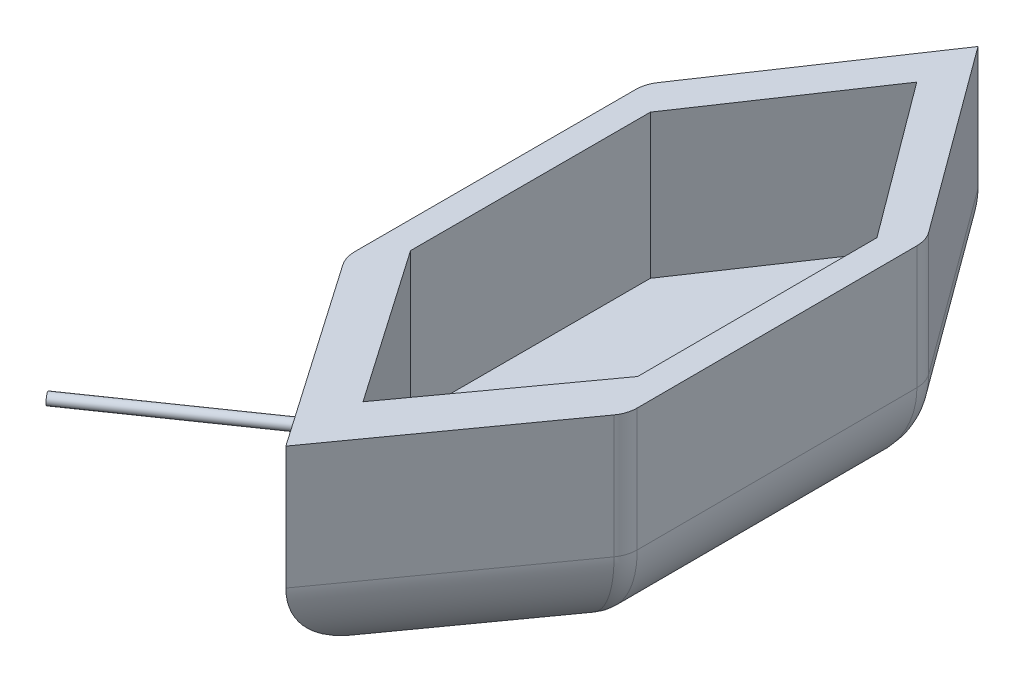
SolidWorks part; units mm, degrees
ref_plane "Front Plane" through (0, 0, 0) normal (0, 0, 1) x (1, 0, 0)
ref_plane "Top Plane" through (0, 0, 0) normal (0, 1, 0) x (1, 0, 0)
ref_plane "Right Plane" through (0, 0, 0) normal (1, 0, 0) x (0, 0, -1)
sketch "Sketch1" plane through (0, 0, 0) normal (0, 1, 0) x (1, 0, 0)
  line L0 (-53.4846, 104.1845) -> (-98.1583, 37.8199)
  line L2 (-6.1312, 39.7046) -> (-53.4846, 104.1845)
  line L3 (-98.1583, 37.8199) -> (-98.1583, -62.1801)
  line L5 (-53.4846, -126.6597) -> (-98.1583, -62.1801)
  line L6 (-5.8888, -60.2951) -> (-53.4846, -126.6597)
  line L7 (-6.1312, 39.7046) -> (-5.8888, -60.2951)
  dimension "D1" = 80
  dimension "D2" = 80
  dimension "D3" = 100
  dimension "D4" = 100
extrude "Boss-Extrude1" add sketch "Sketch1" along normal blind 71 contours L0 L3 L5 L6 L7 L2
sketch "Sketch2" plane through (0, 71, 0) normal (0, 1, 0) x (1, 0, 0)
  line L0 (-53.4193, 83.6901) -> (-89.1583, 30.5984)
  line L1 (-15.1128, 32.1086) -> (-53.4193, 83.6901)
  line L2 (-89.1583, 30.5984) -> (-89.1583, -49.4016)
  line L3 (-53.4193, -100.9853) -> (-89.1583, -49.4016)
  line L4 (-14.9189, -47.8912) -> (-53.4193, -100.9853)
  line L5 (-15.1128, 32.1086) -> (-14.9189, -47.8912)
  line L6 (-6.1312, 39.7046) -> (-5.8888, -60.2951) construction
  line L7 (-98.1583, 37.8199) -> (-98.1583, -62.1801) construction
  dimension "D1" = 9
  dimension "D2" = 9
extrude "Cut-Extrude1" cut sketch "Sketch2" against normal blind 48
fillet "Fillet1" radius 30 6 edges at (-75.8214, 0, 94.4199) (-29.6867, 0, 93.4774) (-75.8214, 0, -71.0022) (-29.8079, 0, -71.9445) (-6.01, 0, 10.2953) (-98.1583, 0, 12.1801)
fillet "Fillet2" radius 10 8 edges at (-89.3715, 8.7868, 59.4335) (-89.3715, 8.7868, -35.138) (-14.9111, 8.7868, -36.8152) (-14.6824, 8.7868, 57.4795) (-98.1583, 50.5, 62.1801) (-98.1583, 50.5, -37.8199) (-6.1312, 50.5, -39.7046) (-5.8888, 50.5, 60.2951)
sketch "Sketch3" plane through (-95.4303, 0, 66.1175) normal (-0.822, 0, 0.5695) x (0.5695, 0, 0.822)
  circle A0 centre (35.9944, 50.5) radius 1.7735
extrude "Boss-Extrude2" add sketch "Sketch3" along normal blind 64
